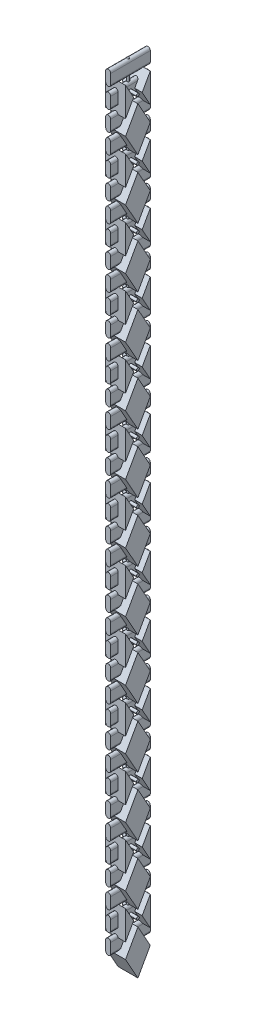
SolidWorks part; units mm, degrees
ref_plane "Front" through (0, 0, 0) normal (0, 0, 1) x (1, 0, 0)
ref_plane "Top" through (0, 0, 0) normal (0, 1, 0) x (1, 0, 0)
ref_plane "Right" through (0, 0, 0) normal (1, 0, 0) x (0, 0, -1)
sketch "Sketch1" plane through (0, 0, 0) normal (1, 0, 0) x (0, 0, -1)
  line L3 (9.525, 0) -> (25.4, 28.3519)
  line L4 (9.525, 0) -> (25.4, -28.3519)
  line L5 (25.4, 28.3519) -> (41.275, 0)
  line L9 (25.4, -28.3519) -> (41.275, 0)
  line L19 (0, 92.4304) -> (0, 0) construction
  line L20 (0, 0) -> (50.8, 0) construction
  line L21 (50.8, 0) -> (50.8, 91.9386) construction
  line L22 (9.525, 19.4963) -> (9.525, 56.7037)
  line L23 (9.525, 56.7037) -> (19.9418, 38.1)
  line L24 (19.9418, 38.1) -> (9.525, 19.4963)
  line L25 (9.525, 76.2) -> (25.4, 104.5519) construction
  line L26 (9.525, 76.2) -> (25.4, 47.8481) construction
  line L27 (25.4, 104.5519) -> (41.275, 76.2) construction
  line L28 (25.4, 47.8481) -> (41.275, 76.2) construction
  line L29 (41.275, 56.7037) -> (41.275, 19.4963)
  line L30 (41.275, 19.4963) -> (30.8582, 38.1)
  line L31 (30.8582, 38.1) -> (41.275, 56.7037)
  dimension "D1" = 50.8
  dimension "D2" = 9.525
  dimension "D3" = 9.525
  dimension "D4" = 9.525
  dimension "D5" = 9.525
  dimension "D6" = 76.2
extrude "Boss-Extrude1" add sketch "Sketch1" along normal blind 25.4
sketch "Sketch2" plane through (0, 0, 0) normal (0, 0, 1) x (1, 0, 0)
  line L0 (12.7, 6.35) -> (12.7, 19.05) construction
  line L1 (9.525, 6.35) -> (9.525, 19.05)
  line L2 (15.875, 6.35) -> (15.875, 19.05)
  line L3 (12.7, 31.75) -> (12.7, 44.45) construction
  line L4 (9.525, 31.75) -> (9.525, 44.45)
  line L5 (15.875, 31.75) -> (15.875, 44.45)
  line L6 (12.7, 57.15) -> (12.7, 69.85) construction
  line L7 (9.525, 57.15) -> (9.525, 69.85)
  line L8 (15.875, 57.15) -> (15.875, 69.85)
  arc A0 (9.525, 6.35) -> (15.875, 6.35) centre (12.7, 6.35) ccw
  arc A1 (15.875, 19.05) -> (9.525, 19.05) centre (12.7, 19.05) ccw
  arc A2 (9.525, 31.75) -> (15.875, 31.75) centre (12.7, 31.75) ccw
  arc A3 (15.875, 44.45) -> (9.525, 44.45) centre (12.7, 44.45) ccw
  arc A4 (9.525, 57.15) -> (15.875, 57.15) centre (12.7, 57.15) ccw
  arc A5 (15.875, 69.85) -> (9.525, 69.85) centre (12.7, 69.85) ccw
  point P2 (12.7, 12.7)
  point P12 (12.7, 38.1)
  point P19 (12.7, 63.5)
  dimension "D3" = 6.35
  dimension "D6" = 25.4
  dimension "D1" = 6.35
  dimension "D2" = 12.7
  dimension "D4" = 12.7
  dimension "D5" = 3
extrude "Boss-Extrude2" add sketch "Sketch2" against normal blind 50.8
sketch "Sketch4" plane through (0, 0, 0) normal (1, 0, 0) x (0, 0, -1)
  circle A0 centre (25.4, 38.1) radius 1.778
  dimension "D2" = 38.1
  dimension "D3" = 3.556
  dimension "D1" = 25.4
extrude "Boss-Extrude4" add sketch "Sketch4" along normal blind 25.4
pattern_linear "LPattern1" count 13 spacing 76.2 along (0, 1, 0) of bodies 172 109 110 108
sketch "Sketch3" plane through (0, 0, 0) normal (0, 1, 0) x (1, 0, 0)
  circle A0 centre (12.7, 25.4) radius 1.5875
  dimension "D1" = 3.175
  dimension "D3" = 12.7
  dimension "D2" = 25.4
extrude "Boss-Extrude3" add sketch "Sketch3" along normal through all
